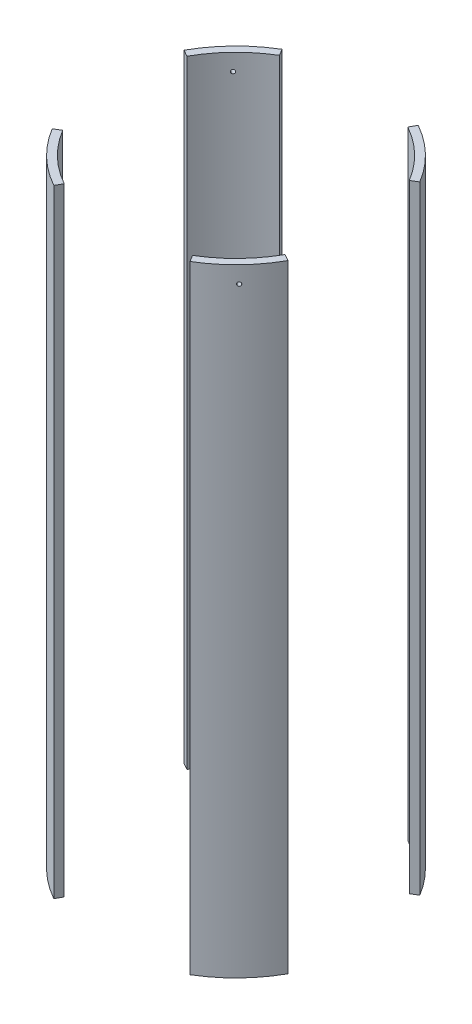
SolidWorks part; units mm, degrees
material "6061-T6 (SS)"
ref_plane "Front Plane" through (0, 0, 0) normal (0, 0, 1) x (1, 0, 0)
ref_plane "Top Plane" through (0, 0, 0) normal (0, 1, 0) x (1, 0, 0)
ref_plane "Right Plane" through (0, 0, 0) normal (1, 0, 0) x (0, 0, -1)
sketch "Sketch2" plane through (0, 0, 0) normal (0, 1, 0) x (1, 0, 0)
  circle A0 centre (0, 0) radius 88.9
  circle A1 centre (0, 0) radius 83.82
  dimension "D1" = 177.8
  dimension "D2" = 167.64
extrude "Boss-Extrude1" add sketch "Sketch2" along normal mid plane 409.8925
sketch "Sketch3" plane through (0, 0, 0) normal (0, 1, 0) x (1, 0, 0)
  line L0 (0, 0) -> (169.6618, 101.6776)
  line L1 (-58.1167, 96.9749) -> (0, 0)
  line L2 (0, 0) -> (53.9, 96.9749)
  line L3 (53.9, 96.9749) -> (-58.1167, 96.9749)
  line L4 (0, 0) -> (70.9917, -118.4586)
  line L5 (70.9917, -118.4586) -> (-65.8409, -118.4586)
  line L6 (-65.8409, -118.4586) -> (0, 0)
  line L7 (169.6618, 101.6776) -> (169.6618, -94.3004)
  line L8 (169.6618, -94.3004) -> (0, 0)
  line L9 (0, 0) -> (-123.7413, 68.7771)
  line L10 (-123.7413, 68.7771) -> (-123.7413, -74.1577)
  line L11 (-123.7413, -74.1577) -> (0, 0)
  dimension "D1" = 60
  dimension "D2" = 60
  dimension "D3" = 60
  dimension "D4" = 60
  dimension "D5" = 30
  dimension "D6" = 30
extrude "Cut-Extrude1" cut sketch "Sketch3" against normal through all both and the other way through all contours L8 L7 L0 | L2 L3 L1 | L10 L11 L9 | L6 L5 L4
ref_plane "Bolt reference plane" through (-56.3092, 0, 58.1758) normal (0.6955, 0, -0.7185) x (-0.7185, 0, -0.6955)
sketch "Sketch5" plane through (-56.3092, 0, 58.1758) normal (0.6955, 0, -0.7185) x (-0.7185, 0, -0.6955)
  circle A0 centre (-0.0228, 193.8338) radius 1.27
  dimension "D1" = 2.54
  dimension "D2" = 21.717
  dimension "D3" = 11.1125
extrude "Top bolt holes" cut sketch "Sketch5" against normal through all
sketch "Sketch6" plane through (0, -204.9462, 0) normal (0, -1, 0) x (-1, 0, 0)
  line L0 (71.8974, -43.0878) -> (40.7211, -73.2638) construction
  line L1 (0, 0) -> (61.8287, -63.8782) construction
  circle A0 centre (60.0621, -62.0531) radius 1.27
  arc A1 (43.189, -77.7041) -> (76.2548, -45.6992) centre (0, 0) ccw construction
  dimension "D2" = 2.54
  dimension "D1" = 86.36
extrude "Bottom bolt holes" cut sketch "Sketch6" against normal blind 31.75
pattern_circular "Bolt pattern" count 4 over 360 about axis through (0, 0, 0) along (0, 1, 0) of "Top bolt holes", "Bottom bolt holes"
equation "\"D1@Boss-Extrude1\"=3*12"
